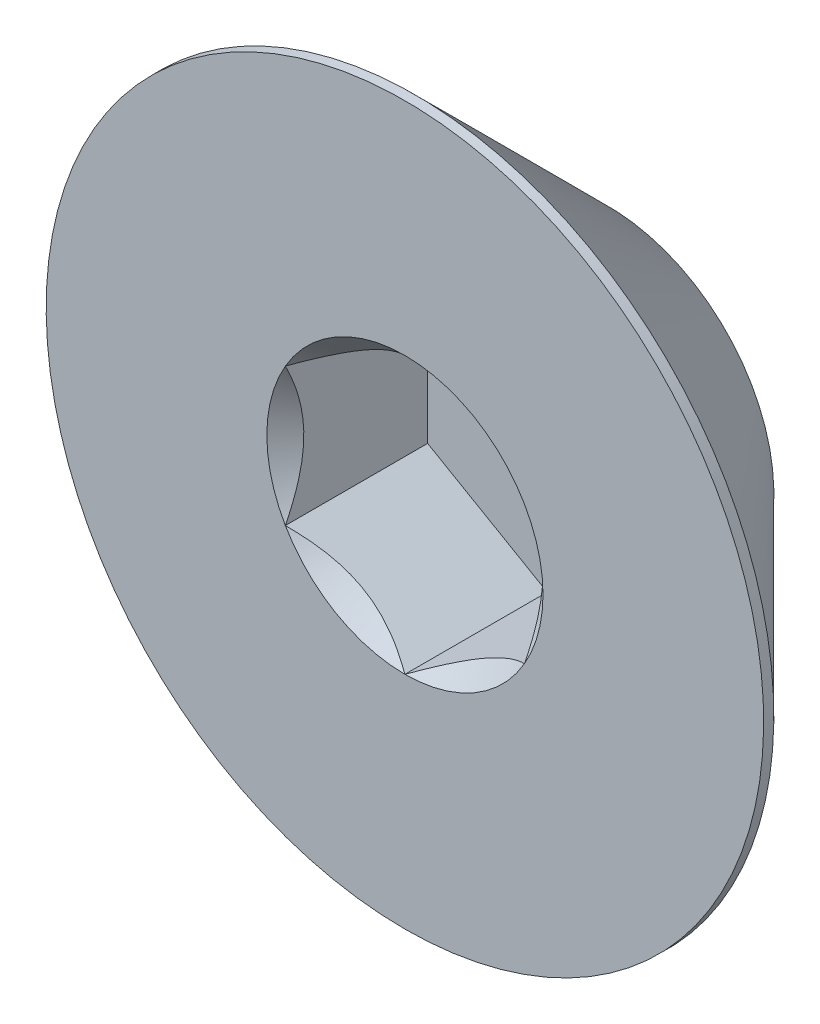
SolidWorks part; units mm, degrees
material "Stainless Steel (ferritic)"
ref_plane "Front" through (0, 0, 0) normal (0, 0, 1) x (1, 0, 0)
ref_plane "Top" through (0, 0, 0) normal (0, 1, 0) x (1, 0, 0)
ref_plane "Right" through (0, 0, 0) normal (1, 0, 0) x (0, 0, -1)
sketch "Sketch11" plane through (0, 0, 0) normal (1, 0, 0) x (0, 0, -1)
  line L0 (-3, 3) -> (3, 3) construction
  line L5 (-3, 3) -> (-3, -3) construction
  line L6 (3, 1.5) -> (3, -1.5) construction
  line L7 (-2.99, 1) -> (-2.99, -1) construction
  line L8 (2.9688, 1.5541) -> (3.4688, 1.5541) construction
  line L9 (3.4688, 1.5541) -> (3.2188, 1.1211) construction
  line L10 (3.2188, 1.1211) -> (2.9688, 1.5541) construction
  line L11 (3.1875, 1.1752) -> (3.25, 1.1752) construction
  line L12 (3.2188, 1.1752) -> (3.2188, 1.1211) construction
  line L13 (2.9844, 1.5271) -> (3.4531, 1.5271) construction
  line L14 (3.2188, 1.5541) -> (3.2188, 1.5) construction
  line L15 (3, 1.5) -> (3.4375, 1.5) construction
  line L17 (-2.915, 3) -> (0.085, 0) construction
  line L18 (0.085, 0) -> (-2.915, -3) construction
  point P3 (-1.3, 3)
  point P8 (0, 3)
  point P21 (3.2188, 1.5271)
  point P26 (-3, 0)
  point P28 (-2.99, 0)
  point P29 (3, 0)
  dimension "Length" = 6
  dimension "Head Diameter" = 6
  dimension "Thread Major Diameter" = 3
  dimension "Head Height" = 1.7
  dimension "Drive Size" = 2
  dimension "Thread Pitch" = 0.5
  dimension "D1" = 0.0625
  dimension "D2" = 0.01
  dimension "D3" = 0.085
  dimension "Countersink Angle" = 90
sketch "Sketch7" plane through (0, 0, 0) normal (1, 0, 0) x (0, 0, -1)
  line L2 (-3, 3) -> (-2.915, 3)
  line L5 (-1.3, 1.385) -> (-1.3, 0)
  line L6 (-3, 3) -> (-3, 0)
  line L8 (-3, 3) -> (-3, -3) construction
  line L9 (-3, 0) -> (-1.3, 0)
  line L12 (-2.915, 3) -> (-1.3, 1.385)
  line L13 (-2.915, 3) -> (0.085, 0) construction
revolve "Revolve2" add sketch "Sketch7" angle 360 mid plane about L9
ref_plane "Plane1" through (0, 0, 1.3) normal (0, 0, 1) x (1, 0, 0)
sketch "Sketch5" plane through (0, 0, 3) normal (0, 0, 1) x (1, 0, 0)
  line L1 (1, -0.5774) -> (1, 0.5774)
  line L2 (1, 0.5774) -> (0, 1.1547)
  line L3 (0, 1.1547) -> (-1, 0.5774)
  line L4 (-1, 0.5774) -> (-1, -0.5774)
  line L5 (-1, -0.5774) -> (0, -1.1547)
  line L6 (0, -1.1547) -> (1, -0.5774)
  circle A0 centre (0, 0) radius 1 construction
extrude "Cut-Extrude2" cut sketch "Sketch5" against normal blind 1.19
sketch "Sketch6" plane through (0, 0, 3) normal (0, 0, -1) x (-1, 0, 0)
  circle A0 centre (0, 0) radius 1.1547
extrude "Cut-Extrude3" cut sketch "Sketch6" along normal blind 1.19 draft 45
equation "\"D1@Cut-Extrude2\"= \"Head Height@Sketch11\" * .7"
equation "\"D1@Cut-Extrude3\" = \"D1@Cut-Extrude2\""
equation "\"D1@Sketch11\"=\"Thread Pitch@Sketch11\"/8"
equation "\"D3@Sketch11\"=\"Head Height@Sketch11\"*.05"
